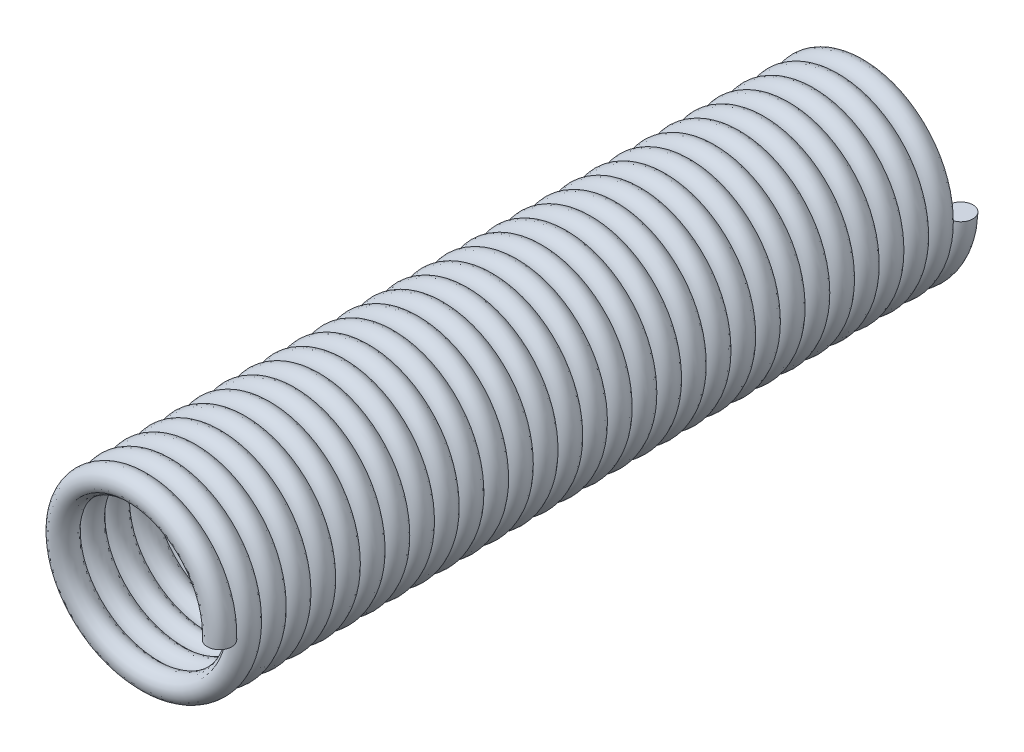
SolidWorks part; units mm, degrees
ref_plane "Front Plane" through (0, 0, 0) normal (0, 0, 1) x (1, 0, 0)
ref_plane "Top Plane" through (0, 0, 0) normal (0, 1, 0) x (1, 0, 0)
ref_plane "Right Plane" through (0, 0, 0) normal (1, 0, 0) x (0, 0, -1)
sketch "Sketch1" plane through (0, 0, 0) normal (0, 0, 1) x (1, 0, 0)
  line L0 (0, 0) -> (6.35, 0) construction
  circle A0 centre (0, 0) radius 6.35 construction
  circle A1 centre (5.5499, 0) radius 0.8001 construction
  circle A2 centre (0, 0) radius 5.5499
  dimension "D1" = 1.6002
  dimension "D2" = 12.7
curve "Helix/Spiral1" pitch 1.6256 height 48.768 turns 30
sketch "Sketch2" plane through (0, 0, 0) normal (0, 1, 0) x (1, 0, 0)
  circle A0 centre (5.5499, 0) radius 0.8001
  spline S0 degree 3 poles (5.5499, 0) (5.5499, 0.0336) (5.2609, 0.1017) (4.0265, 0.2032) (2.1791, 0.3048) (0, 0.4064) (-2.1791, 0.508) (-4.0265, 0.6096) (-5.2609, 0.7112) (-5.6944, 0.8128) (-5.2609, 0.9144) (-4.0265, 1.016) (-1.5634, 1.1515) (1.5634, 1.2869) (4.0265, 1.4224) (5.2609, 1.524) (5.6944, 1.6256) (5.2609, 1.7272) (4.0265, 1.8288) (1.5634, 1.9643) (-1.5634, 2.0997) (-4.0265, 2.2352) (-5.2609, 2.3368) (-5.6944, 2.4384) (-5.2609, 2.54) (-4.0265, 2.6416) (-1.5634, 2.7771) (1.5634, 2.9125) (4.0265, 3.048) (5.2609, 3.1496) (5.6944, 3.2512) (5.2609, 3.3528) (4.0265, 3.4544) (1.5634, 3.5899) (-1.5634, 3.7253) (-4.0265, 3.8608) (-5.2609, 3.9624) (-5.6944, 4.064) (-5.2609, 4.1656) (-4.0265, 4.2672) (-1.5634, 4.4027) (1.5634, 4.5381) (4.0265, 4.6736) (5.2609, 4.7752) (5.6944, 4.8768) (5.2609, 4.9784) (4.0265, 5.08) (1.5634, 5.2155) (-1.5634, 5.3509) (-4.0265, 5.4864) (-5.2609, 5.588) (-5.6944, 5.6896) (-5.2609, 5.7912) (-4.0265, 5.8928) (-1.5634, 6.0283) (1.5634, 6.1637) (4.0265, 6.2992) (5.2609, 6.4008) (5.6944, 6.5024) (5.2609, 6.604) (4.0265, 6.7056) (1.5634, 6.8411) (-1.5634, 6.9765) (-4.0265, 7.112) (-5.2609, 7.2136) (-5.6944, 7.3152) (-5.2609, 7.4168) (-4.0265, 7.5184) (-1.5634, 7.6539) (1.5634, 7.7893) (4.0265, 7.9248) (5.2609, 8.0264) (5.6944, 8.128) (5.2609, 8.2296) (4.0265, 8.3312) (1.5634, 8.4667) (-1.5634, 8.6021) (-4.0265, 8.7376) (-5.2609, 8.8392) (-5.6944, 8.9408) (-5.2609, 9.0424) (-4.0265, 9.144) (-1.5634, 9.2795) (1.5634, 9.4149) (4.0265, 9.5504) (5.2609, 9.652) (5.6944, 9.7536) (5.2609, 9.8552) (4.0265, 9.9568) (1.5634, 10.0923) (-1.5634, 10.2277) (-4.0265, 10.3632) (-5.2609, 10.4648) (-5.6944, 10.5664) (-5.2609, 10.668) (-4.0265, 10.7696) (-1.5634, 10.9051) (1.5634, 11.0405) (4.0265, 11.176) (5.2609, 11.2776) (5.6944, 11.3792) (5.2609, 11.4808) (4.0265, 11.5824) (1.5634, 11.7179) (-1.5634, 11.8533) (-4.0265, 11.9888) (-5.2609, 12.0904) (-5.6944, 12.192) (-5.2609, 12.2936) (-4.0265, 12.3952) (-1.5634, 12.5307) (1.5634, 12.6661) (4.0265, 12.8016) (5.2609, 12.9032) (5.6944, 13.0048) (5.2609, 13.1064) (4.0265, 13.208) (1.5634, 13.3435) (-1.5634, 13.4789) (-4.0265, 13.6144) (-5.2609, 13.716) (-5.6944, 13.8176) (-5.2609, 13.9192) (-4.0265, 14.0208) (-1.5634, 14.1563) (1.5634, 14.2917) (4.0265, 14.4272) (5.2609, 14.5288) (5.6944, 14.6304) (5.2609, 14.732) (4.0265, 14.8336) (1.5634, 14.9691) (-1.5634, 15.1045) (-4.0265, 15.24) (-5.2609, 15.3416) (-5.6944, 15.4432) (-5.2609, 15.5448) (-4.0265, 15.6464) (-1.5634, 15.7819) (1.5634, 15.9173) (4.0265, 16.0528) (5.2609, 16.1544) (5.6944, 16.256) (5.2609, 16.3576) (4.0265, 16.4592) (1.5634, 16.5947) (-1.5634, 16.7301) (-4.0265, 16.8656) (-5.2609, 16.9672) (-5.6944, 17.0688) (-5.2609, 17.1704) (-4.0265, 17.272) (-1.5634, 17.4075) (1.5634, 17.5429) (4.0265, 17.6784) (5.2609, 17.78) (5.6944, 17.8816) (5.2609, 17.9832) (4.0265, 18.0848) (1.5634, 18.2203) (-1.5634, 18.3557) (-4.0265, 18.4912) (-5.2609, 18.5928) (-5.6944, 18.6944) (-5.2609, 18.796) (-4.0265, 18.8976) (-1.5634, 19.0331) (1.5634, 19.1685) (4.0265, 19.304) (5.2609, 19.4056) (5.6944, 19.5072) (5.2609, 19.6088) (4.0265, 19.7104) (1.5634, 19.8459) (-1.5634, 19.9813) (-4.0265, 20.1168) (-5.2609, 20.2184) (-5.6944, 20.32) (-5.2609, 20.4216) (-4.0265, 20.5232) (-1.5634, 20.6587) (1.5634, 20.7941) (4.0265, 20.9296) (5.2609, 21.0312) (5.6944, 21.1328) (5.2609, 21.2344) (4.0265, 21.336) (1.5634, 21.4715) (-1.5634, 21.6069) (-4.0265, 21.7424) (-5.2609, 21.844) (-5.6944, 21.9456) (-5.2609, 22.0472) (-4.0265, 22.1488) (-1.5634, 22.2843) (1.5634, 22.4197) (4.0265, 22.5552) (5.2609, 22.6568) (5.6944, 22.7584) (5.2609, 22.86) (4.0265, 22.9616) (1.5634, 23.0971) (-1.5634, 23.2325) (-4.0265, 23.368) (-5.2609, 23.4696) (-5.6944, 23.5712) (-5.2609, 23.6728) (-4.0265, 23.7744) (-1.5634, 23.9099) (1.5634, 24.0453) (4.0265, 24.1808) (5.2609, 24.2824) (5.6944, 24.384) (5.2609, 24.4856) (4.0265, 24.5872) (1.5634, 24.7227) (-1.5634, 24.8581) (-4.0265, 24.9936) (-5.2609, 25.0952) (-5.6944, 25.1968) (-5.2609, 25.2984) (-4.0265, 25.4) (-1.5634, 25.5355) (1.5634, 25.6709) (4.0265, 25.8064) (5.2609, 25.908) (5.6944, 26.0096) (5.2609, 26.1112) (4.0265, 26.2128) (1.5634, 26.3483) (-1.5634, 26.4837) (-4.0265, 26.6192) (-5.2609, 26.7208) (-5.6944, 26.8224) (-5.2609, 26.924) (-4.0265, 27.0256) (-1.5634, 27.1611) (1.5634, 27.2965) (4.0265, 27.432) (5.2609, 27.5336) (5.6944, 27.6352) (5.2609, 27.7368) (4.0265, 27.8384) (1.5634, 27.9739) (-1.5634, 28.1093) (-4.0265, 28.2448) (-5.2609, 28.3464) (-5.6944, 28.448) (-5.2609, 28.5496) (-4.0265, 28.6512) (-1.5634, 28.7867) (1.5634, 28.9221) (4.0265, 29.0576) (5.2609, 29.1592) (5.6944, 29.2608) (5.2609, 29.3624) (4.0265, 29.464) (1.5634, 29.5995) (-1.5634, 29.7349) (-4.0265, 29.8704) (-5.2609, 29.972) (-5.6944, 30.0736) (-5.2609, 30.1752) (-4.0265, 30.2768) (-1.5634, 30.4123) (1.5634, 30.5477) (4.0265, 30.6832) (5.2609, 30.7848) (5.6944, 30.8864) (5.2609, 30.988) (4.0265, 31.0896) (1.5634, 31.2251) (-1.5634, 31.3605) (-4.0265, 31.496) (-5.2609, 31.5976) (-5.6944, 31.6992) (-5.2609, 31.8008) (-4.0265, 31.9024) (-1.5634, 32.0379) (1.5634, 32.1733) (4.0265, 32.3088) (5.2609, 32.4104) (5.6944, 32.512) (5.2609, 32.6136) (4.0265, 32.7152) (1.5634, 32.8507) (-1.5634, 32.9861) (-4.0265, 33.1216) (-5.2609, 33.2232) (-5.6944, 33.3248) (-5.2609, 33.4264) (-4.0265, 33.528) (-1.5634, 33.6635) (1.5634, 33.7989) (4.0265, 33.9344) (5.2609, 34.036) (5.6944, 34.1376) (5.2609, 34.2392) (4.0265, 34.3408) (1.5634, 34.4763) (-1.5634, 34.6117) (-4.0265, 34.7472) (-5.2609, 34.8488) (-5.6944, 34.9504) (-5.2609, 35.052) (-4.0265, 35.1536) (-1.5634, 35.2891) (1.5634, 35.4245) (4.0265, 35.56) (5.2609, 35.6616) (5.6944, 35.7632) (5.2609, 35.8648) (4.0265, 35.9664) (1.5634, 36.1019) (-1.5634, 36.2373) (-4.0265, 36.3728) (-5.2609, 36.4744) (-5.6944, 36.576) (-5.2609, 36.6776) (-4.0265, 36.7792) (-1.5634, 36.9147) (1.5634, 37.0501) (4.0265, 37.1856) (5.2609, 37.2872) (5.6944, 37.3888) (5.2609, 37.4904) (4.0265, 37.592) (1.5634, 37.7275) (-1.5634, 37.8629) (-4.0265, 37.9984) (-5.2609, 38.1) (-5.6944, 38.2016) (-5.2609, 38.3032) (-4.0265, 38.4048) (-1.5634, 38.5403) (1.5634, 38.6757) (4.0265, 38.8112) (5.2609, 38.9128) (5.6944, 39.0144) (5.2609, 39.116) (4.0265, 39.2176) (1.5634, 39.3531) (-1.5634, 39.4885) (-4.0265, 39.624) (-5.2609, 39.7256) (-5.6944, 39.8272) (-5.2609, 39.9288) (-4.0265, 40.0304) (-1.5634, 40.1659) (1.5634, 40.3013) (4.0265, 40.4368) (5.2609, 40.5384) (5.6944, 40.64) (5.2609, 40.7416) (4.0265, 40.8432) (1.5634, 40.9787) (-1.5634, 41.1141) (-4.0265, 41.2496) (-5.2609, 41.3512) (-5.6944, 41.4528) (-5.2609, 41.5544) (-4.0265, 41.656) (-1.5634, 41.7915) (1.5634, 41.9269) (4.0265, 42.0624) (5.2609, 42.164) (5.6944, 42.2656) (5.2609, 42.3672) (4.0265, 42.4688) (1.5634, 42.6043) (-1.5634, 42.7397) (-4.0265, 42.8752) (-5.2609, 42.9768) (-5.6944, 43.0784) (-5.2609, 43.18) (-4.0265, 43.2816) (-1.5634, 43.4171) (1.5634, 43.5525) (4.0265, 43.688) (5.2609, 43.7896) (5.6944, 43.8912) (5.2609, 43.9928) (4.0265, 44.0944) (1.5634, 44.2299) (-1.5634, 44.3653) (-4.0265, 44.5008) (-5.2609, 44.6024) (-5.6944, 44.704) (-5.2609, 44.8056) (-4.0265, 44.9072) (-1.5634, 45.0427) (1.5634, 45.1781) (4.0265, 45.3136) (5.2609, 45.4152) (5.6944, 45.5168) (5.2609, 45.6184) (4.0265, 45.72) (1.5634, 45.8555) (-1.5634, 45.9909) (-4.0265, 46.1264) (-5.2609, 46.228) (-5.6944, 46.3296) (-5.2609, 46.4312) (-4.0265, 46.5328) (-1.5634, 46.6683) (1.5634, 46.8037) (4.0265, 46.9392) (5.2609, 47.0408) (5.6944, 47.1424) (5.2609, 47.244) (4.0265, 47.3456) (1.5634, 47.4811) (-1.5634, 47.6165) (-4.0265, 47.752) (-5.2609, 47.8536) (-5.6944, 47.9552) (-5.2609, 48.0568) (-4.0265, 48.1584) (-2.1791, 48.26) (0, 48.3616) (2.1791, 48.4632) (4.0265, 48.5648) (5.2609, 48.6663) (5.5499, 48.7344) (5.5499, 48.768) knots 0 0 0 0 0.002083 0.004167 0.00625 0.008333 0.010417 0.0125 0.014583 0.016667 0.01875 0.020833 0.022917 0.027083 0.029167 0.03125 0.033333 0.035417 0.0375 0.039583 0.04375 0.045833 0.047917 0.05 0.052083 0.054167 0.05625 0.060417 0.0625 0.064583 0.066667 0.06875 0.070833 0.072917 0.077083 0.079167 0.08125 0.083333 0.085417 0.0875 0.089583 0.09375 0.095833 0.097917 0.1 0.102083 0.104167 0.10625 0.110417 0.1125 0.114583 0.116667 0.11875 0.120833 0.122917 0.127083 0.129167 0.13125 0.133333 0.135417 0.1375 0.139583 0.14375 0.145833 0.147917 0.15 0.152083 0.154167 0.15625 0.160417 0.1625 0.164583 0.166667 0.16875 0.170833 0.172917 0.177083 0.179167 0.18125 0.183333 0.185417 0.1875 0.189583 0.19375 0.195833 0.197917 0.2 0.202083 0.204167 0.20625 0.210417 0.2125 0.214583 0.216667 0.21875 0.220833 0.222917 0.227083 0.229167 0.23125 0.233333 0.235417 0.2375 0.239583 0.24375 0.245833 0.247917 0.25 0.252083 0.254167 0.25625 0.260417 0.2625 0.264583 0.266667 0.26875 0.270833 0.272917 0.277083 0.279167 0.28125 0.283333 0.285417 0.2875 0.289583 0.29375 0.295833 0.297917 0.3 0.302083 0.304167 0.30625 0.310417 0.3125 0.314583 0.316667 0.31875 0.320833 0.322917 0.327083 0.329167 0.33125 0.333333 0.335417 0.3375 0.339583 0.34375 0.345833 0.347917 0.35 0.352083 0.354167 0.35625 0.360417 0.3625 0.364583 0.366667 0.36875 0.370833 0.372917 0.377083 0.379167 0.38125 0.383333 0.385417 0.3875 0.389583 0.39375 0.395833 0.397917 0.4 0.402083 0.404167 0.40625 0.410417 0.4125 0.414583 0.416667 0.41875 0.420833 0.422917 0.427083 0.429167 0.43125 0.433333 0.435417 0.4375 0.439583 0.44375 0.445833 0.447917 0.45 0.452083 0.454167 0.45625 0.460417 0.4625 0.464583 0.466667 0.46875 0.470833 0.472917 0.477083 0.479167 0.48125 0.483333 0.485417 0.4875 0.489583 0.49375 0.495833 0.497917 0.5 0.502083 0.504167 0.50625 0.510417 0.5125 0.514583 0.516667 0.51875 0.520833 0.522917 0.527083 0.529167 0.53125 0.533333 0.535417 0.5375 0.539583 0.54375 0.545833 0.547917 0.55 0.552083 0.554167 0.55625 0.560417 0.5625 0.564583 0.566667 0.56875 0.570833 0.572917 0.577083 0.579167 0.58125 0.583333 0.585417 0.5875 0.589583 0.59375 0.595833 0.597917 0.6 0.602083 0.604167 0.60625 0.610417 0.6125 0.614583 0.616667 0.61875 0.620833 0.622917 0.627083 0.629167 0.63125 0.633333 0.635417 0.6375 0.639583 0.64375 0.645833 0.647917 0.65 0.652083 0.654167 0.65625 0.660417 0.6625 0.664583 0.666667 0.66875 0.670833 0.672917 0.677083 0.679167 0.68125 0.683333 0.685417 0.6875 0.689583 0.69375 0.695833 0.697917 0.7 0.702083 0.704167 0.70625 0.710417 0.7125 0.714583 0.716667 0.71875 0.720833 0.722917 0.727083 0.729167 0.73125 0.733333 0.735417 0.7375 0.739583 0.74375 0.745833 0.747917 0.75 0.752083 0.754167 0.75625 0.760417 0.7625 0.764583 0.766667 0.76875 0.770833 0.772917 0.777083 0.779167 0.78125 0.783333 0.785417 0.7875 0.789583 0.79375 0.795833 0.797917 0.8 0.802083 0.804167 0.80625 0.810417 0.8125 0.814583 0.816667 0.81875 0.820833 0.822917 0.827083 0.829167 0.83125 0.833333 0.835417 0.8375 0.839583 0.84375 0.845833 0.847917 0.85 0.852083 0.854167 0.85625 0.860417 0.8625 0.864583 0.866667 0.86875 0.870833 0.872917 0.877083 0.879167 0.88125 0.883333 0.885417 0.8875 0.889583 0.89375 0.895833 0.897917 0.9 0.902083 0.904167 0.90625 0.910417 0.9125 0.914583 0.916667 0.91875 0.920833 0.922917 0.927083 0.929167 0.93125 0.933333 0.935417 0.9375 0.939583 0.94375 0.945833 0.947917 0.95 0.952083 0.954167 0.95625 0.960417 0.9625 0.964583 0.966667 0.96875 0.970833 0.972917 0.977083 0.979167 0.98125 0.983333 0.985417 0.9875 0.989583 0.991667 0.99375 0.995833 0.997917 1 1 1 1 construction
  dimension "D1" = 1.6002
sweep "Sweep1" add profiles "Sketch2" path "Helix/Spiral1"
